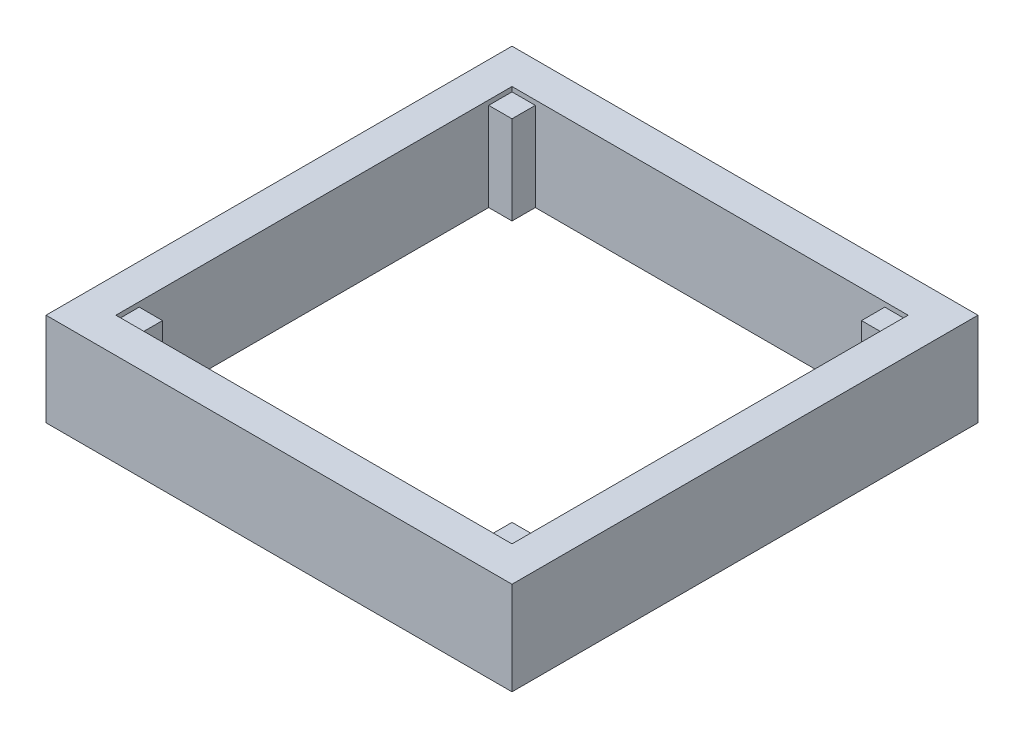
SolidWorks part; units mm, degrees
material "Pine"
ref_plane "Front Plane" through (0, 0, 0) normal (0, 0, 1) x (1, 0, 0)
ref_plane "Top Plane" through (0, 0, 0) normal (0, 1, 0) x (1, 0, 0)
ref_plane "Right Plane" through (0, 0, 0) normal (1, 0, 0) x (0, 0, -1)
sketch "Sketch2" plane through (0, 0, 0) normal (0, 1, 0) x (1, 0, 0)
  line L0 (0, 54.078) -> (0, -67.5911) construction
  line L1 (-107.95, -127) -> (-127, -127)
  line L2 (-107.95, -127) -> (-107.95, 127)
  line L3 (-107.95, 127) -> (-127, 127)
  line L4 (-127, -127) -> (-127, 127)
  line L5 (-127, 127) -> (127, 127)
  line L6 (-127, 127) -> (-127, 107.95)
  line L7 (-127, 107.95) -> (127, 107.95)
  line L8 (127, 127) -> (127, 107.95)
  line L9 (127, 127) -> (107.95, 127)
  line L10 (127, 127) -> (127, -127)
  line L11 (127, -127) -> (107.95, -127)
  line L12 (107.95, 127) -> (107.95, -127)
  line L13 (127, -127) -> (-127, -127)
  line L14 (127, -127) -> (127, -107.95)
  line L15 (127, -107.95) -> (-127, -107.95)
  line L16 (-127, -127) -> (-127, -107.95)
  line L17 (-95.2622, 0) -> (90.2193, 0) construction
  line L18 (-107.95, -95.25) -> (-95.25, -95.25)
  line L19 (-107.95, 107.95) -> (-95.25, 107.95)
  line L20 (-107.95, 107.95) -> (-107.95, 95.25)
  line L21 (-107.95, 95.25) -> (-95.25, 95.25)
  line L22 (-95.25, 107.95) -> (-95.25, 95.25)
  line L23 (-95.25, -107.95) -> (-95.25, -95.25)
  line L24 (107.95, -95.25) -> (95.25, -95.25)
  line L25 (95.25, -107.95) -> (95.25, -95.25)
  line L26 (95.25, 107.95) -> (95.25, 95.25)
  line L27 (107.95, 95.25) -> (95.25, 95.25)
  dimension "D1" = 19.05
  dimension "D2" = 254
  dimension "D3" = 127
  dimension "D4" = 127
  dimension "D5" = 12.7
sketch "Sketch3" plane through (0, 0, 0) normal (0, 1, 0) x (1, 0, 0)
  line L0 (-107.95, -127) -> (-107.95, 127) construction
  line L1 (-127, 107.95) -> (-107.95, 107.95)
  line L2 (-127, 107.95) -> (-127, -107.95)
  line L3 (-127, -107.95) -> (-107.95, -107.95)
  line L4 (-107.95, 107.95) -> (-107.95, -107.95)
  line L5 (127, -107.95) -> (-127, -107.95) construction
extrude "Boss-Extrude1" add sketch "Sketch3" along normal blind 50.8
sketch "Sketch5" plane through (0, 0, 0) normal (0, 1, 0) x (1, 0, 0)
  line L1 (-127, -107.95) -> (127, -107.95)
  line L2 (-127, -107.95) -> (-127, -127)
  line L3 (-127, -127) -> (127, -127)
  line L4 (127, -107.95) -> (127, -127)
extrude "Boss-Extrude2" add sketch "Sketch5" along normal up to surface (50.8 mm away) up to face at (-117.475, 50.8, 0)
sketch "Sketch6" plane through (0, 0, 0) normal (0, 1, 0) x (1, 0, 0)
  line L0 (-107.95, -127) -> (-107.95, 127) construction
  line L1 (-95.25, -95.25) -> (-107.95, -95.25)
  line L2 (-95.25, -95.25) -> (-95.25, -107.95)
  line L3 (-95.25, -107.95) -> (-107.95, -107.95)
  line L4 (-107.95, -95.25) -> (-107.95, -107.95)
extrude "Boss-Extrude3" add sketch "Sketch6" along normal offset from surface (48.26 mm away) 2.54 up to face at (-16.4042, 50.8, 60.325)
mirror "Mirror2" about plane through (0, 0, 0) normal (1, 0, 0) of "Boss-Extrude3", "Boss-Extrude1"
mirror "Mirror3" about plane through (0, 0, 0) normal (0, 0, 1) of "Mirror2", "Boss-Extrude3", "Boss-Extrude2"
